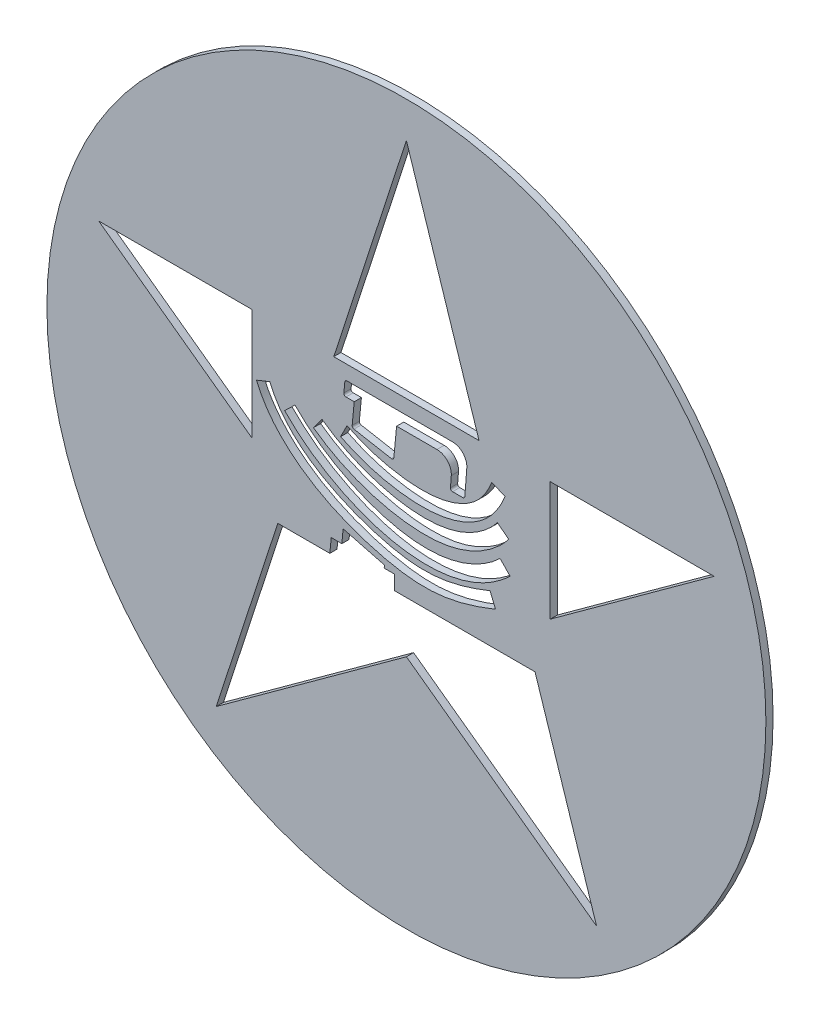
SolidWorks part; units mm, degrees
ref_plane "Front" through (0, 0, 0) normal (0, 0, 1) x (1, 0, 0)
ref_plane "Top" through (0, 0, 0) normal (0, 1, 0) x (1, 0, 0)
ref_plane "Right" through (0, 0, 0) normal (1, 0, 0) x (0, 0, -1)
sketch "草图1" plane through (0, 0, 0) normal (0, 0, 1) x (1, 0, 0)
  line L0 (0, 4.5) -> (-1.0103, 1.3906)
  line L1 (1.7204, -1.0058) -> (1.7889, -1.0058)
  line L2 (-1.8991, 0.6449) -> (-2.0848, 0.5709)
  line L3 (1.0103, 1.3906) -> (-1.0103, 1.3906)
  line L4 (1.1634, -0.3417) -> (1.2391, -0.5268)
  line L5 (0, -1.7188) -> (2.645, -3.6406)
  line L6 (2, -0.2658) -> (4.2798, 1.3906)
  line L7 (-2.15, 1.3906) -> (-2.15, -0.0666)
  line L8 (2, 1.3906) -> (2, -0.0227)
  line L9 (-1.7889, -1.0058) -> (1.7204, -1.0058)
  line L10 (-2.15, 1.3906) -> (-4.2798, 1.3906)
  line L11 (-0.8701, 1.0234) -> (-0.8566, 1.1635)
  line L12 (-0.88, -0.6173) -> (-0.3052, -0.7668)
  line L13 (-1.7889, -1.0058) -> (-2.645, -3.6406)
  line L14 (-0.8268, 1.1906) -> (0.6405, 1.1906)
  line L15 (-1.0457, -0.8058) -> (-1.0649, -1.0058)
  line L16 (-1.197, -1.0058) -> (-0.1678, -1.0058)
  line L17 (35.5655, 121.6074) -> (206.2322, 121.6074) construction
  line L18 (0.783, 0.5906) -> (0.6425, 0.5906)
  line L19 (1.0103, 1.3906) -> (0, 4.5)
  line L20 (0.8129, 0.6183) -> (0.8399, 0.9755)
  line L21 (-0.1678, -0.8058) -> (-0.3089, -0.8058)
  line L22 (-0.8403, 0.9906) -> (-0.7257, 0.9906)
  line L23 (-0.7257, 0.9906) -> (-0.7545, 0.6906)
  line L24 (-0.73, 0.6582) -> (-0.21, 0.564)
  line L25 (-0.1749, 0.5906) -> (-0.1365, 0.9906)
  line L26 (0.6127, 0.6228) -> (0.6179, 0.6917)
  line L27 (-0.1365, 0.9906) -> (0.1859, 0.9906)
  line L28 (-1.0457, -0.8058) -> (-0.8981, -0.8058)
  line L29 (-0.1678, -1.0058) -> (-0.1678, -0.8058)
  line L30 (0.6179, 0.6917) -> (0.6242, 0.7755)
  line L31 (0.1859, 0.9906) -> (0.4248, 0.9906)
  line L32 (-0.88, -0.6173) -> (-0.8981, -0.8058)
  line L33 (-0.3052, -0.7668) -> (-0.3089, -0.8058)
  line L34 (1.3026, 0.1165) -> (1.442, -0.0269)
  line L35 (-1.5498, 0.5383) -> (-1.6936, 0.3993)
  line L36 (-1.1752, 0.5556) -> (-1.2928, 0.3939)
  line L37 (1.2651, 0.53) -> (1.4232, 0.4076)
  line L38 (1.1849, 0.9722) -> (1.3723, 0.9024)
  line L39 (-2.645, -3.6406) -> (0, -1.7188)
  line L40 (4.2798, 1.3906) -> (2, 1.3906)
  line L41 (-0.825, 0.6532) -> (-0.9152, 0.4747)
  line L42 (-4.2798, 1.3906) -> (-2.15, -0.1568)
  line L43 (2.645, -3.6406) -> (1.7889, -1.0058)
  line L44 (-2.15, 1.3906) -> (-2.15, -0.1568)
  line L45 (2, 1.3906) -> (2, -0.2658)
  circle A0 centre (0, 0) radius 5
  arc A1 (0.6242, 0.7755) -> (0.4248, 0.9906) centre (0.4248, 0.7906) ccw
  arc A2 (0.8399, 0.9755) -> (0.6405, 1.1906) centre (0.6405, 0.9906) ccw
  arc A6 (-0.8566, 1.1635) -> (-0.8268, 1.1906) centre (-0.8268, 1.1606) cw
  arc A7 (-0.8701, 1.0234) -> (-0.8403, 0.9906) centre (-0.8403, 1.0205) ccw
  arc A8 (-0.7545, 0.6906) -> (-0.73, 0.6582) centre (-0.7247, 0.6877) ccw
  arc A9 (-0.21, 0.564) -> (-0.1749, 0.5906) centre (-0.2047, 0.5934) ccw
  arc A10 (0.6425, 0.5906) -> (0.6127, 0.6228) centre (0.6425, 0.6205) cw
  arc A11 (0.8129, 0.6183) -> (0.783, 0.5906) centre (0.783, 0.6205) cw
  spline S0 degree 1 poles (-0.9152, 0.4747) (1.3723, 0.9024) knots 0 0 1 1 construction
  spline S1 degree 3 poles (-0.8701, 0.564) (-0.2093, 0.23) (0.9573, 0.0747) (1.2786, 0.9373) knots 0 0 0 0 1 1 1 1
  spline S2 degree 3 poles (-0.9152, 0.4747) (-0.7282, 0.3802) (-0.3413, 0.2414) (0.3466, 0.161) (0.8775, 0.2996) (1.2093, 0.5772) (1.3314, 0.7924) (1.3723, 0.9024) knots 0 0 0 0 0.25 0.5 0.75 0.875 1 1 1 1
  spline S3 degree 3 poles (-1.234, 0.4747) (-0.5245, -0.0414) (0.7397, -0.3123) (1.3441, 0.4688) knots 0 0 0 0 1 1 1 1
  spline S4 degree 1 poles (-1.2928, 0.3939) (1.4232, 0.4076) knots 0 0 1 1 construction
  spline S5 degree 3 poles (-1.6217, 0.4688) (-0.91, -0.2674) (0.5364, -0.7675) (1.3723, 0.0448) knots 0 0 0 0 1 1 1 1
  spline S6 degree 3 poles (-1.2928, 0.3939) (-1.0971, 0.2515) (-0.6736, 0.0269) (0.0908, -0.1554) (0.8342, -0.0919) (1.2715, 0.2116) (1.4232, 0.4076) knots 0 0 0 0 0.25 0.5 0.75 1 1 1 1
  spline S7 degree 3 poles (-1.992, 0.6079) (-1.7406, -0.0223) (-0.2617, -0.7384) (0.565, -0.6941) (1.2013, -0.4342) knots 0 0 0 0 0.484817 1 1 1 1
  spline S8 degree 1 poles (-1.6936, 0.3993) (1.442, -0.0269) knots 0 0 1 1 construction
  spline S9 degree 3 poles (-1.6936, 0.3993) (-1.4979, 0.1969) (-1.0496, -0.1373) (-0.1971, -0.4731) (0.5407, -0.4963) (1.0841, -0.3111) (1.3349, -0.131) (1.442, -0.0269) knots 0 0 0 0 0.25 0.5 0.75 0.875 1 1 1 1
  spline S10 degree 1 poles (-2.0848, 0.5709) (1.2391, -0.5268) knots 0 0 1 1 construction
  spline S11 degree 3 poles (-2.0848, 0.5709) (-1.9515, 0.2364) (-1.3998, -0.3134) (-0.3981, -0.6951) (0.2537, -0.785) (0.784, -0.6946) (1.0943, -0.5859) (1.2391, -0.5268) knots 0 0 0 0 0.25 0.5 0.75 0.875 1 1 1 1
  spline S12 degree 1 poles (-0.825, 0.6532) (1.1849, 0.9722) knots 0 0 1 1 construction
  spline S13 degree 3 poles (-0.825, 0.6532) (-0.6522, 0.5659) (-0.2948, 0.4376) (0.3409, 0.3647) (0.791, 0.489) (1.0514, 0.7066) (1.1516, 0.8829) (1.1849, 0.9722) knots 0 0 0 0 0.25 0.5 0.75 0.875 1 1 1 1
  spline S14 degree 1 poles (-1.1752, 0.5556) (1.2651, 0.53) knots 0 0 1 1 construction
  spline S15 degree 3 poles (-1.1752, 0.5556) (-0.9939, 0.4238) (-0.6025, 0.2162) (0.1102, 0.0464) (0.7716, 0.1083) (1.1363, 0.3636) (1.2651, 0.53) knots 0 0 0 0 0.25 0.5 0.75 1 1 1 1
  spline S16 degree 1 poles (-1.5498, 0.5383) (1.3026, 0.1165) knots 0 0 1 1 construction
  spline S17 degree 3 poles (-1.5498, 0.5383) (-1.3678, 0.3501) (-0.953, 0.0399) (-0.1491, -0.2731) (0.6443, -0.3032) (1.1212, -0.0598) (1.3026, 0.1165) knots 0 0 0 0 0.25 0.5 0.75 1 1 1 1
  spline S18 degree 1 poles (-1.8991, 0.6449) (1.1634, -0.3417) knots 0 0 1 1 construction
  spline S19 degree 3 poles (-1.8991, 0.6449) (-1.7807, 0.3482) (-1.3046, -0.1277) (-0.3367, -0.5045) (0.2529, -0.5811) (0.7296, -0.5013) (1.0267, -0.3975) (1.1634, -0.3417) knots 0 0 0 0 0.25 0.5 0.75 0.875 1 1 1 1
  dimension "D1" = 10
  dimension "D5" = 0.2
  dimension "D6" = 0.2
  dimension "D2" = 0.2
  dimension "D7" = 3.6817
  dimension "D8" = 0.2
  dimension "D3" = 0.2
  dimension "D4" = 0.2
  dimension "D9" = 0.6
  dimension "D10" = 0.3
  dimension "D11" = 0.4
  dimension "D16" = 0.2
  dimension "D12" = 0.1
  dimension "D13" = 0.1
extrude "凸台-拉伸3" add sketch "草图1" along normal blind 0.1 contours A0 L7 L44 L42 L10 L19 L3 L0 L43 L5 L39 L13 L9 L15 L28 L32 L12 L33 L21 L29 L1 L45 L8 L40 L6 L20 A11 L18 A10 L26 L30 A1 L31 L27 L25 A9 L24 A8 L23 L22 A7 L11 A6 L14
